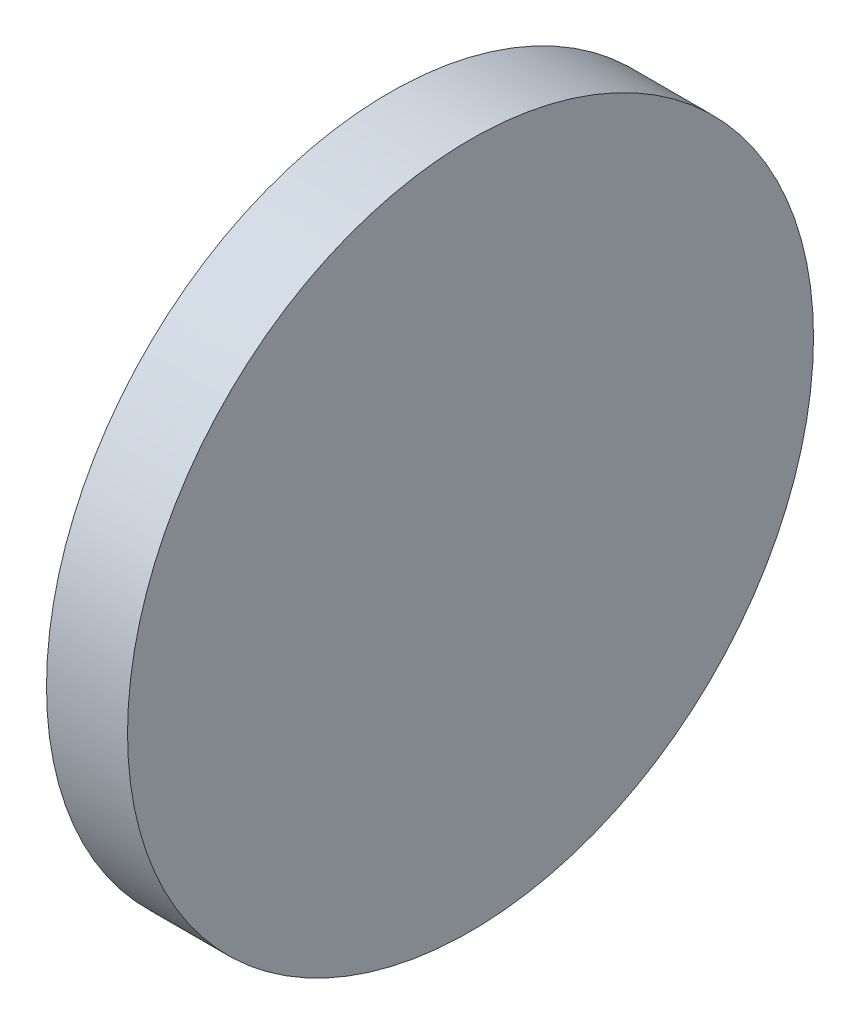
SolidWorks part; units mm, degrees
ref_plane "前视基准面" through (0, 0, 0) normal (0, 0, 1) x (1, 0, 0)
ref_plane "上视基准面" through (0, 0, 0) normal (0, 1, 0) x (1, 0, 0)
ref_plane "右视基准面" through (0, 0, 0) normal (1, 0, 0) x (0, 0, -1)
sketch "草图1" plane through (0, 0, 0) normal (0, 0, 1) x (1, 0, 0)
  line L0 (0, 12.7) -> (0, 0)
  line L2 (0, 12.7) -> (3, 12.7)
  line L3 (0, 0) -> (3, 0)
  line L4 (3, 12.7) -> (3, 0)
  dimension "D1" = 12.7
  dimension "D2" = 3
revolve "旋转2" add sketch "草图1" angle 360 about L3
